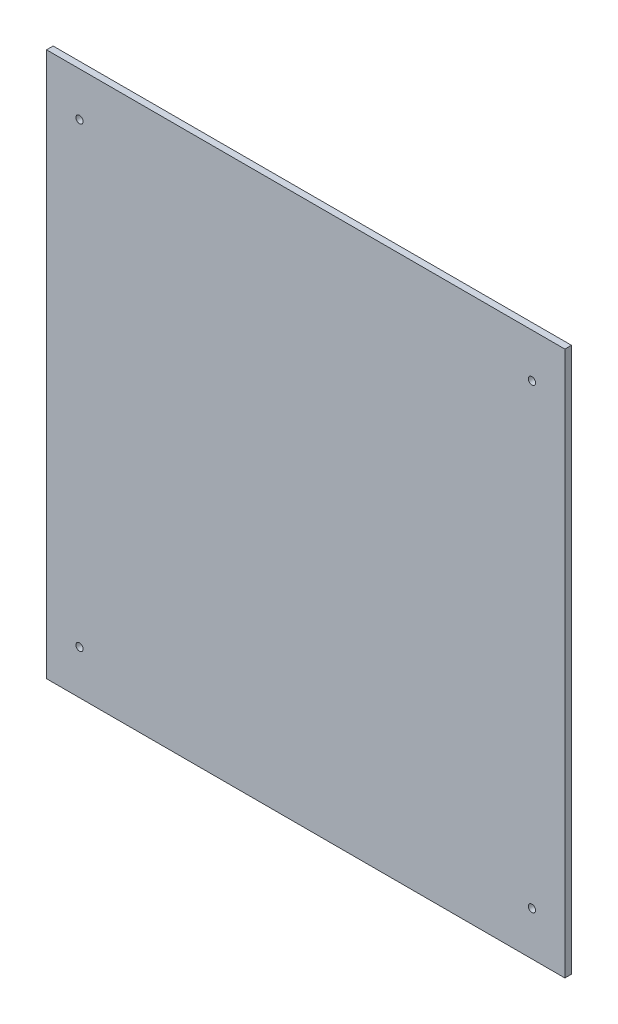
SolidWorks part; units mm, degrees
ref_plane "Plan de face" through (0, 0, 0) normal (0, 0, 1) x (1, 0, 0)
ref_plane "Plan de dessus" through (0, 0, 0) normal (0, 1, 0) x (1, 0, 0)
ref_plane "Plan de droite" through (0, 0, 0) normal (1, 0, 0) x (0, 0, -1)
sketch "Esquisse1" plane through (0, 0, 0) normal (0, 0, 1) x (1, 0, 0)
  line L1 (0, 0) -> (236, 0)
  line L2 (0, 0) -> (0, 248)
  line L3 (0, 248) -> (236, 248)
  line L4 (236, 0) -> (236, 248)
  dimension "D1" = 248
  dimension "D2" = 236
extrude "Boss.-Extru.1" add sketch "Esquisse1" along normal blind 3
sketch "Esquisse2" plane through (0, 0, 3) normal (0, 0, 1) x (1, 0, 0)
  line L0 (236, 248) -> (0, 248) construction
  line L1 (0, 248) -> (0, 0) construction
  line L2 (118, 248) -> (118, 0) construction
  line L3 (0, 0) -> (236, 0) construction
  line L4 (0, 124) -> (236, 124) construction
  line L5 (236, 0) -> (236, 248) construction
  circle A0 centre (15, 228) radius 1.65
  circle A1 centre (221, 228) radius 1.65
  circle A2 centre (221, 20) radius 1.65
  circle A3 centre (15, 20) radius 1.65
  dimension "D1" = 3.3
  dimension "D2" = 20
  dimension "D3" = 15
extrude "Enlèv. mat.-Extru.1" cut sketch "Esquisse2" against normal through all
